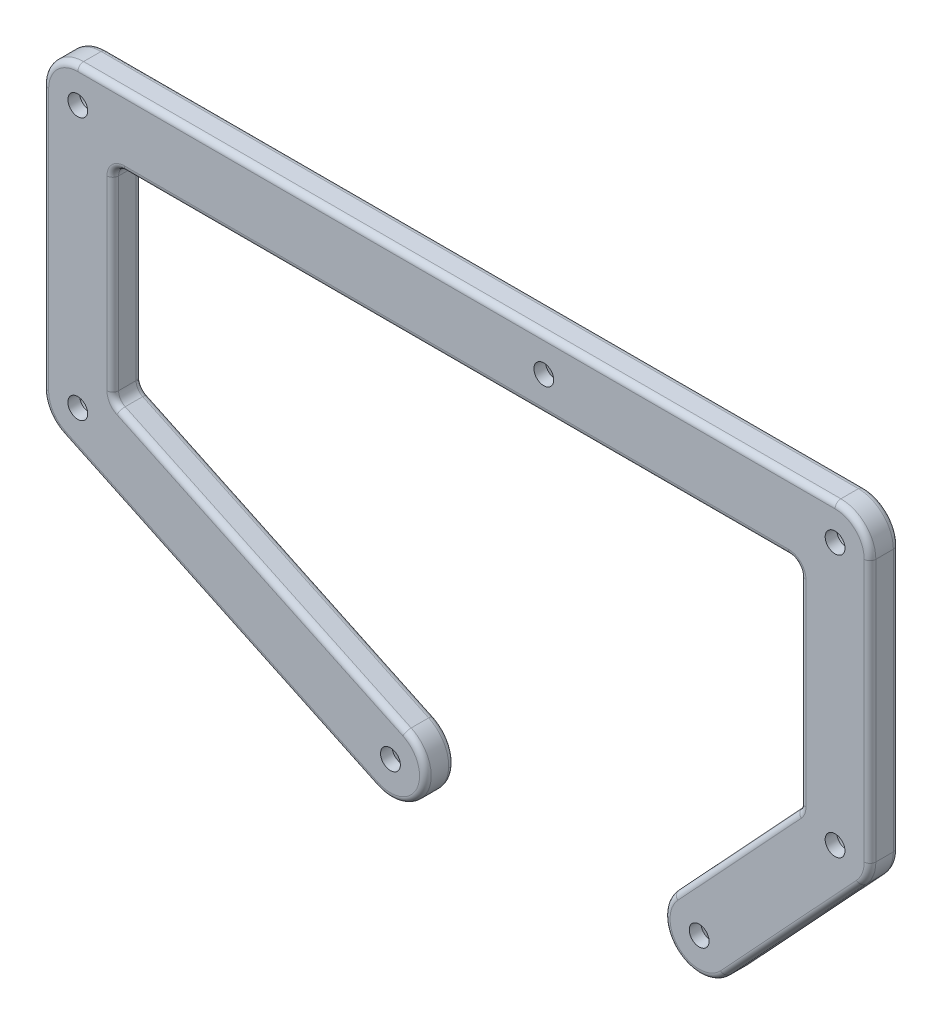
SolidWorks part; units mm, degrees
ref_plane "Plan de face" through (0, 0, 0) normal (0, 0, 1) x (1, 0, 0)
ref_plane "Plan de dessus" through (0, 0, 0) normal (0, 1, 0) x (1, 0, 0)
ref_plane "Plan de droite" through (0, 0, 0) normal (1, 0, 0) x (0, 0, -1)
sketch "Esquisse2" plane through (0, 0, 0) normal (0, 0, 1) x (1, 0, 0)
  line L0 (0, 70.1) -> (0, 0) construction
  line L1 (26.67, 0) -> (-26.33, 0) construction
  line L2 (-26.33, 0) -> (-26.33, -0.28) construction
  line L3 (-80, 70.1) -> (50, 70.1) construction
  line L4 (-80, 25.1) -> (50, 25.1) construction
  line L5 (50, 70.1) -> (50, 25.1) construction
  line L8 (-80, 76.1) -> (50, 76.1)
  line L9 (56, 70.1) -> (56, 25.1)
  line L13 (-86, 70.1) -> (-86, 25.1)
  line L14 (-74, 31.1) -> (-74, 64.1)
  line L15 (-74, 64.1) -> (44, 64.1)
  line L19 (44, 64.1) -> (44, 27.4578)
  line L20 (-80, 31.1) -> (-74, 31.1) construction
  line L23 (-74, 31.1) -> (-74, 25.1) construction
  line L24 (-74, 70.1) -> (-74, 64.1) construction
  line L25 (-80, 64.1) -> (-74, 64.1) construction
  line L26 (50, 64.1) -> (44, 64.1) construction
  line L27 (44, 70.1) -> (44, 64.1) construction
  line L28 (-82.565, 19.6759) -> (-28.895, -5.7041)
  line L29 (54.3948, 21.0151) -> (31.0648, -4.0849)
  line L30 (22.2752, 4.0849) -> (45.6052, 29.1849) construction
  line L31 (22.2752, 4.0849) -> (44, 27.4578)
  line L32 (-23.765, 5.1441) -> (-77.435, 30.5241) construction
  line L33 (-23.765, 5.1441) -> (-74, 28.8997)
  line L34 (-74, 31.1) -> (-74, 28.8997)
  circle A0 centre (0, 70.1) radius 1.7
  circle A1 centre (-26.33, -0.28) radius 1.7
  circle A2 centre (26.67, 0) radius 1.7
  circle A3 centre (0, 70.1) radius 6 construction
  circle A4 centre (-26.33, -0.28) radius 6 construction
  circle A5 centre (26.67, 0) radius 6 construction
  circle A20 centre (-80, 25.1) radius 1.7
  circle A21 centre (-80, 25.1) radius 6 construction
  circle A22 centre (50, 25.1) radius 1.7
  circle A23 centre (50, 25.1) radius 6 construction
  circle A24 centre (50, 70.1) radius 1.7
  circle A25 centre (50, 70.1) radius 6 construction
  circle A26 centre (-80, 70.1) radius 1.7
  circle A27 centre (-80, 70.1) radius 6 construction
  arc A28 (-86, 25.1) -> (-82.565, 19.6759) centre (-80, 25.1) ccw
  arc A29 (-23.765, 5.1441) -> (-28.895, -5.7041) centre (-26.33, -0.28) cw
  arc A30 (22.2752, 4.0849) -> (31.0648, -4.0849) centre (26.67, 0) ccw
  arc A31 (56, 25.1) -> (54.3948, 21.0151) centre (50, 25.1) cw
  arc A32 (50, 76.1) -> (56, 70.1) centre (50, 70.1) cw
  arc A33 (-86, 70.1) -> (-80, 76.1) centre (-80, 70.1) cw
  dimension "D1" = 3.4
  dimension "D2" = 12
  dimension "D8" = 12
  dimension "D9" = 3.4
  dimension "D11" = 3.4
  dimension "D12" = 12
  dimension "D7" = 3.4
  dimension "D10" = 12
  dimension "D13" = 3.4
  dimension "D14" = 12
  dimension "D3" = 0.28
  dimension "D4" = 53
  dimension "D5" = 70.1
  dimension "D6" = 26.67
  dimension "D15" = 130
  dimension "D16" = 45
  dimension "D17" = 50
extrude "Boss.-Extru.1" add sketch "Esquisse2" against normal blind 5
sketch "Esquisse3" plane through (0, 0, 0) normal (0, 0, 1) x (1, 0, 0)
  line L0 (-27.9754, 2.57) -> (-24.6846, 2.57)
  line L1 (-24.6846, 2.57) -> (-23.0391, -0.28)
  line L2 (-23.0391, -0.28) -> (-24.6846, -3.13)
  line L3 (-24.6846, -3.13) -> (-27.9754, -3.13)
  line L4 (-27.9754, -3.13) -> (-29.6209, -0.28)
  line L5 (-29.6209, -0.28) -> (-27.9754, 2.57)
  line L6 (-29.6209, -0.28) -> (-23.0391, -0.28) construction
  line L7 (25.0246, 2.85) -> (28.3154, 2.85)
  line L8 (28.3154, 2.85) -> (29.9609, 0)
  line L9 (29.9609, 0) -> (28.3154, -2.85)
  line L10 (28.3154, -2.85) -> (25.0246, -2.85)
  line L11 (25.0246, -2.85) -> (23.3791, 0)
  line L12 (23.3791, 0) -> (25.0246, 2.85)
  line L13 (23.3791, 0) -> (29.9609, 0) construction
  line L14 (-1.6454, 72.95) -> (1.6454, 72.95)
  line L15 (1.6454, 72.95) -> (3.2909, 70.1)
  line L16 (3.2909, 70.1) -> (1.6454, 67.25)
  line L17 (1.6454, 67.25) -> (-1.6454, 67.25)
  line L18 (-1.6454, 67.25) -> (-3.2909, 70.1)
  line L19 (-3.2909, 70.1) -> (-1.6454, 72.95)
  line L20 (-3.2909, 70.1) -> (3.2909, 70.1) construction
  circle A0 centre (-80, 70.1) radius 3.25
  circle A1 centre (-80, 25.1) radius 3.25
  circle A2 centre (50, 25.1) radius 3.25
  circle A3 centre (50, 70.1) radius 3.25
  point P14 (26.67, 0)
  point P19 (-26.33, -0.28)
  point P20 (-26.33, -0.28)
  point P21 (26.67, 0)
  point P22 (-24.6846, -3.13)
  point P23 (0, 70.1)
  point P42 (0, 70.1)
  dimension "D1" = 6.5
  dimension "D2" = 120
  dimension "D3" = 5.7
  dimension "D4" = 120
  dimension "D5" = 5.7
  dimension "D6" = 120
  dimension "D7" = 5.7
extrude "Enlèv. mat.-Extru.1" cut sketch "Esquisse3" along normal blind 3 from surface at -5 starting at face at (-78.3, 70.1, -5)
fillet "Congé1" radius 2 4 edges at (44, 27.4578, -2.5) (-74, 28.8997, -2.5) (-74, 64.1, -2.5) (44, 64.1, -2.5)
fillet "Congé2" radius 1 40 edges at (54.2426, 74.3426, 0) (56, 47.6, 0) (55.5843, 22.9055, 0) (42.7298, 8.4651, 0) (22.5851, -4.3948, 0) (32.8701, 15.4835, 0) (43.8614, 27.5123, 0) (44, 45.1719, 0) (43.4142, 63.5142, 0) (-15, 64.1, 0) (-73.4142, 63.5142, 0) (-74, 46.1331, 0) (-73.6897, 29.0962, 0) (-48.31, 16.7512, 0) (-20.9059, -2.845, 0) (-55.73, 6.9859, 0) (-85.069, 21.8899, 0) (-86, 47.6, 0) (-84.2426, 74.3426, 0) (54.2426, 74.3426, -5) (56, 47.6, -5) (55.5843, 22.9055, -5) (42.7298, 8.4651, -5) (22.5851, -4.3948, -5) (32.8701, 15.4835, -5) (43.8614, 27.5123, -5) (44, 45.1719, -5) (43.4142, 63.5142, -5) (-15, 64.1, -5) (-73.4142, 63.5142, -5) (-74, 46.1331, -5) (-73.6897, 29.0962, -5) (-48.31, 16.7512, -5) (-20.9059, -2.845, -5) (-55.73, 6.9859, -5) (-85.069, 21.8899, -5) (-86, 47.6, -5) (-84.2426, 74.3426, -5) (-15, 76.1, 0) (-15, 76.1, -5)
